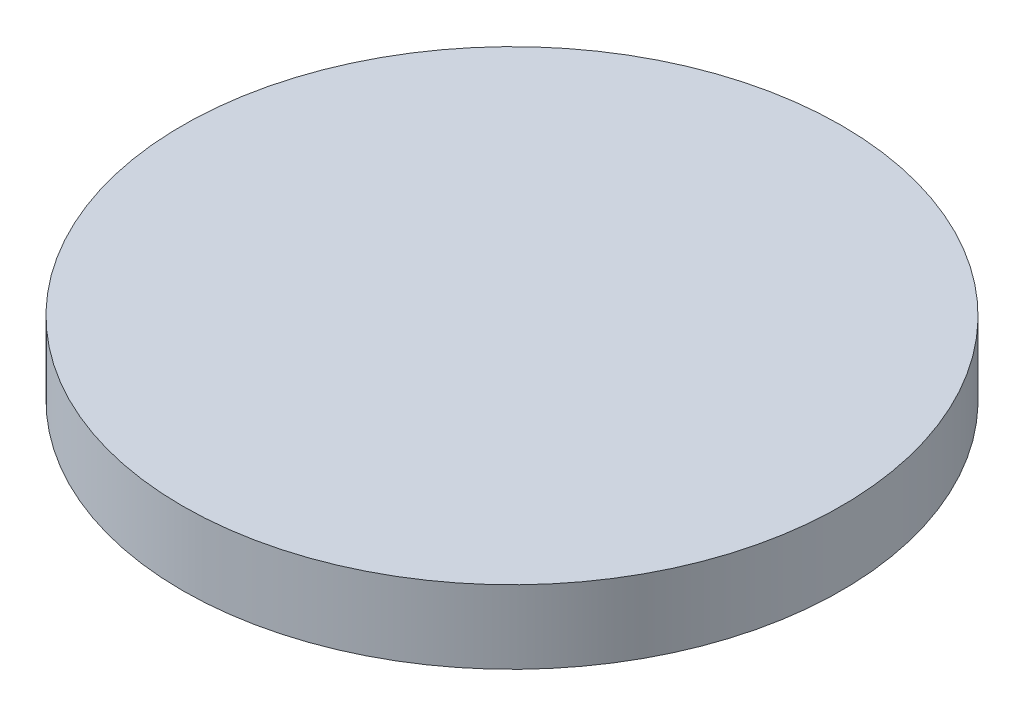
SolidWorks part; units mm, degrees
ref_plane "Front Plane" through (0, 0, 0) normal (0, 0, 1) x (1, 0, 0)
ref_plane "Top Plane" through (0, 0, 0) normal (0, 1, 0) x (1, 0, 0)
ref_plane "Right Plane" through (0, 0, 0) normal (1, 0, 0) x (0, 0, -1)
sketch "Sketch1" plane through (0, 0, 0) normal (0, 1, 0) x (1, 0, 0)
  circle A0 centre (0, 0) radius 45
  dimension "D1" = 90
extrude "Boss-Extrude1" add sketch "Sketch1" along normal blind 10
